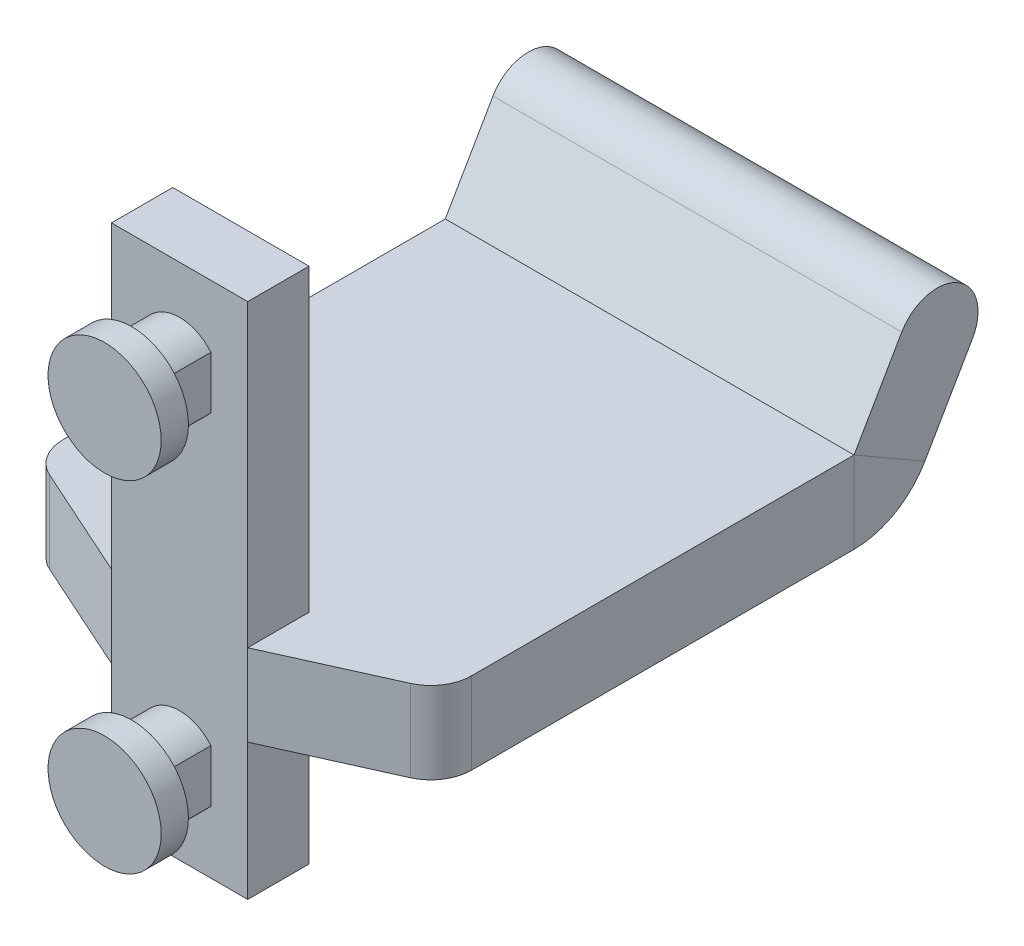
SolidWorks part; units mm, degrees
ref_plane "Front Plane" through (0, 0, 0) normal (0, 0, 1) x (1, 0, 0)
ref_plane "Top Plane" through (0, 0, 0) normal (0, 1, 0) x (1, 0, 0)
ref_plane "Right Plane" through (0, 0, 0) normal (1, 0, 0) x (0, 0, -1)
sketch "草图1" plane through (0, 0, 0) normal (0, 0, 1) x (1, 0, 0)
  line L0 (-2.3, 1.9261) -> (-2.3, -1.9261)
  line L3 (2.3, 1.9261) -> (2.3, -1.9261)
  line L4 (-2.3, -23.0739) -> (-2.3, -26.9261)
  line L5 (2.3, -23.0739) -> (2.3, -26.9261)
  arc A0 (-2.3, -1.9261) -> (2.3, -1.9261) centre (0, 0) ccw
  arc A1 (2.3, 1.9261) -> (-2.3, 1.9261) centre (0, 0) ccw
  arc A2 (-2.3, -26.9261) -> (2.3, -26.9261) centre (0, -25) ccw
  arc A3 (2.3, -23.0739) -> (-2.3, -23.0739) centre (0, -25) ccw
  dimension "D1" = 3
  dimension "D4" = 3
  dimension "D2" = 4.6
  dimension "D3" = 4.6
  dimension "D5" = 25
  dimension "D6" = 2.3
  dimension "D7" = 2.3
extrude "凸台-拉伸1" add sketch "草图1" along normal blind 3.5
sketch "草图2" plane through (0, 0, 3.5) normal (0, 0, 1) x (1, 0, 0)
  circle A0 centre (0, 0) radius 4.15
  circle A1 centre (0, -25) radius 4.15
  arc A2 (2.3, -23.0739) -> (-2.3, -23.0739) centre (0, -25) ccw construction
  dimension "D1" = 8.3
  dimension "D2" = 8.3
extrude "凸台-拉伸2" add sketch "草图2" along normal blind 2
sketch "草图3" plane through (0, 0, 0) normal (0, 0, -1) x (-1, 0, 0)
  line L1 (-5, 6.5) -> (5, 6.5)
  line L2 (-5, 6.5) -> (-5, -31.5)
  line L3 (-5, -31.5) -> (5, -31.5)
  line L4 (5, 6.5) -> (5, -31.5)
  dimension "D1" = 38
  dimension "D2" = 10
  dimension "D3" = 5
  dimension "D4" = 6.5
extrude "凸台-拉伸3" add sketch "草图3" along normal blind 4.5
sketch "草图5" plane through (0, 0, -4.5) normal (0, 0, -1) x (-1, 0, 0)
  line L1 (-15, -15.5) -> (15, -15.5)
  line L2 (-15, -15.5) -> (-15, -21.5)
  line L3 (-15, -21.5) -> (15, -21.5)
  line L4 (15, -15.5) -> (15, -21.5)
  line L5 (-5, -31.5) -> (5, -31.5) construction
  line L6 (-5, 6.5) -> (-5, -31.5) construction
  line L7 (5, -31.5) -> (5, 6.5) construction
  dimension "D1" = 10
  dimension "D2" = 10
  dimension "D3" = 10
  dimension "D4" = 6
extrude "凸台-拉伸4" add sketch "草图5" along normal blind 25
sketch "草图8" plane through (0, -15.5, 0) normal (0, 1, 0) x (1, 0, 0)
  line L0 (15, 4.5) -> (5, 4.5)
  line L1 (5, 4.5) -> (5, 0)
  line L2 (5, 0) -> (15, 4.5)
  line L3 (-15, 4.5) -> (-5, 4.5)
  line L4 (-5, 4.5) -> (-5, 0)
  line L5 (-5, 0) -> (-15, 4.5)
extrude "凸台-拉伸5" add sketch "草图8" against normal blind 6
sketch "草图9" plane through (0, 0, 0) normal (1, 0, 0) x (0, 0, -1)
  line L0 (29.5, -18.5) -> (34.5, -18.5)
  line L1 (29.5, -15.5) -> (29.5, -21.5) construction
  line L2 (37.0981, -17) -> (40.5981, -10.9378)
  arc A0 (34.5, -18.5) -> (37.0981, -17) centre (34.5, -15.5) ccw
  dimension "D2" = 3
  dimension "D1" = 5
  dimension "D3" = 7
  dimension "D4" = 60
sketch "草图10" plane through (0, 0, -29.5) normal (0, 0, -1) x (-1, 0, 0)
  line L1 (-15, -15.5) -> (15, -15.5)
  line L2 (-15, -15.5) -> (-15, -21.5)
  line L3 (-15, -21.5) -> (15, -21.5)
  line L4 (15, -15.5) -> (15, -21.5)
sweep "扫描1" add profiles "草图10" path "草图9"
sketch "草图11" plane through (0, 9.3761, -5.4133) normal (0, 0.866, -0.5) x (1, 0, 0)
  line L0 (15, 37.6279) -> (15, 43.6279) construction
  line L1 (15, 40.6279) -> (-15, 40.6279)
  line L2 (15, 40.6279) -> (15, 43.6279)
  line L3 (15, 43.6279) -> (-15, 43.6279)
  line L4 (-15, 40.6279) -> (-15, 43.6279)
revolve "旋转1" add sketch "草图11" angle 180 about L1
fillet "圆角1" radius 3 2 edges at (-15, -18.5, -4.5) (15, -18.5, -4.5)
